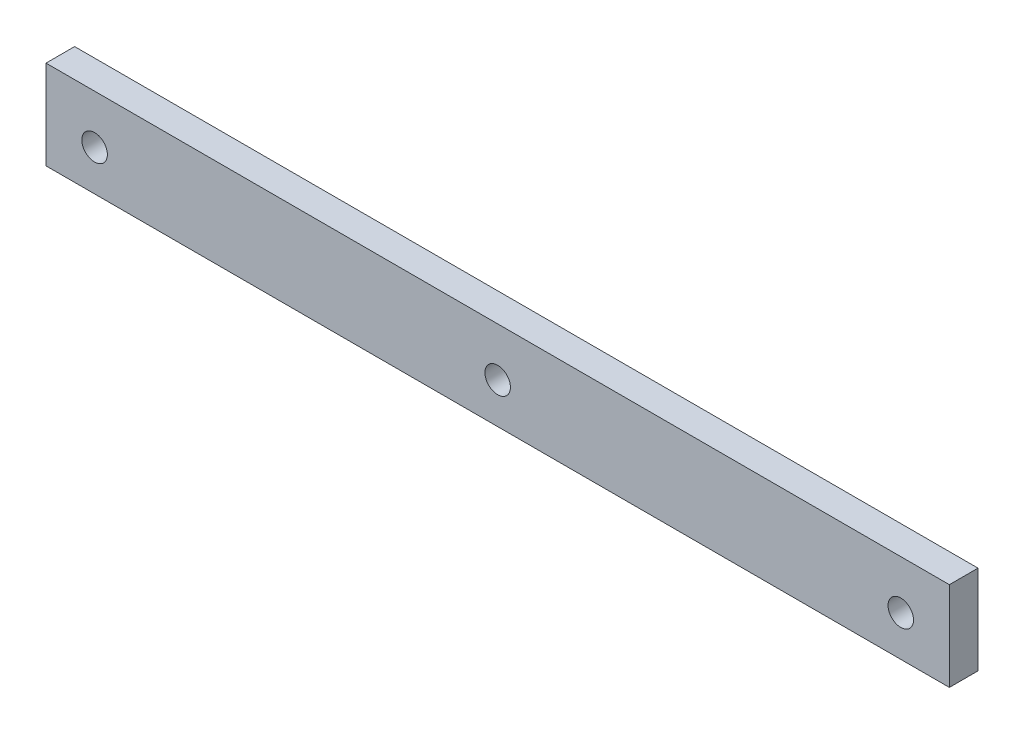
SolidWorks part; units mm, degrees
material "Maple"
ref_plane "Front Plane" through (0, 0, 0) normal (0, 0, 1) x (1, 0, 0)
ref_plane "Top Plane" through (0, 0, 0) normal (0, 1, 0) x (1, 0, 0)
ref_plane "Right Plane" through (0, 0, 0) normal (1, 0, 0) x (0, 0, -1)
sketch "Sketch1" plane through (0, 0, 0) normal (0, 0, 1) x (1, 0, 0)
  line L1 (-50.085, 4.935) -> (50.085, 4.935)
  line L2 (-50.085, 4.935) -> (-50.085, -4.935)
  line L3 (-50.085, -4.935) -> (50.085, -4.935)
  line L4 (50.085, 4.935) -> (50.085, -4.935)
  line L5 (-50.085, 4.935) -> (50.085, -4.935) construction
  line L6 (-50.085, -4.935) -> (50.085, 4.935) construction
  point P0 (0, 0)
  dimension "D1" = 100.17
  dimension "D2" = 9.87
extrude "Boss-Extrude1" add sketch "Sketch1" along normal blind 3.175
sketch "Sketch2" plane through (0, 0, 3.175) normal (0, 0, 1) x (1, 0, 0)
  line L0 (-44.6967, -0.4533) -> (-50, 4.85) construction
  line L2 (0, 0) -> (0, -2.7111) construction
  line L8 (-50, 4.85) -> (-50, -4.935)
  line L9 (50.085, 4.85) -> (-50, 4.85)
  line L10 (-50, 4.85) -> (-50, -4.935) construction
  line L11 (50.085, 4.85) -> (-50, 4.85) construction
  circle A0 centre (-44.6967, -0.4533) radius 1.415
  circle A1 centre (44.6967, -0.4533) radius 1.415
  dimension "D3" = 2.83
  dimension "D1" = 7.5
  dimension "D4" = 0.085
extrude "Cut-Extrude1" cut sketch "Sketch2" against normal through all
sketch "Sketch3" plane through (0, 0, 3.175) normal (0, 0, 1) x (1, 0, 0)
  line L0 (-44.6967, -0.4533) -> (44.6967, -0.4533) construction
  circle A0 centre (0, -0.4533) radius 1.415
  dimension "D1" = 2.83
extrude "Cut-Extrude2" cut sketch "Sketch3" against normal through all
equation "\"length\"=100"
equation "\"D1@Sketch1\"=\"length\" + 2*\"kerf\""
equation "\"width\"=9.7"
equation "\"D2@Sketch1\"=\"width\" + 2*\"kerf\""
equation "\"depth\"=10"
equation "\"kerf\"= 0.17 / 2"
